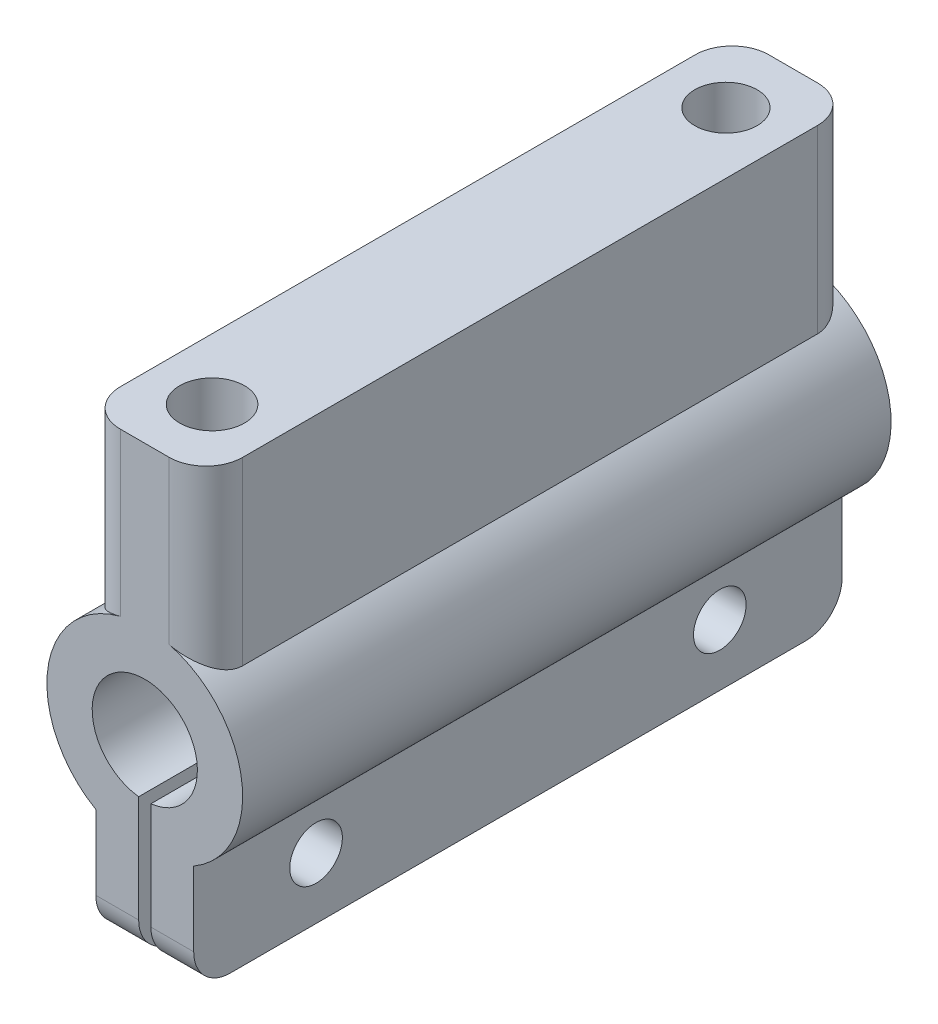
SolidWorks part; units mm, degrees
material "Ti-5Al-2.5Sn Annealed (SS)"
ref_plane "前视基准面" through (0, 0, 0) normal (0, 0, 1) x (1, 0, 0)
ref_plane "上视基准面" through (0, 0, 0) normal (0, 1, 0) x (1, 0, 0)
ref_plane "右视基准面" through (0, 0, 0) normal (1, 0, 0) x (0, 0, -1)
other "Configuration Table"
sketch "Sketch1" plane through (0, 0, 0) normal (0, 0, 1) x (1, 0, 0)
  line L0 (-8, 25) -> (0, 25)
  line L1 (-8, 25) -> (-8, 9)
  line L2 (-8, 9) -> (0, 9)
  line L3 (0, 25) -> (0, 9)
  line L4 (-4.5, 9) -> (-3.5, 9)
  line L5 (-4.5, 9) -> (-4.5, 25)
  line L6 (-4.5, 25) -> (-3.5, 25)
  line L7 (-3.5, 9) -> (-3.5, 25)
  line L8 (-9, 31.245) -> (1, 31.245)
  line L9 (1, 31.245) -> (1, 46)
  line L10 (1, 46) -> (-9, 46)
  line L11 (-9, 46) -> (-9, 31.245)
  circle A0 centre (-4, 25) radius 8
  circle A1 centre (-4, 25) radius 4.3
  point P11 (-4, 9)
  dimension "D1" = 16
  dimension "D2" = 8.6
  dimension "D3" = 3.5
  dimension "D4" = 4
  dimension "D5" = 8
  dimension "D6" = 25
  dimension "D7" = 16
  dimension "D8" = 10
  dimension "D9" = 14.755
extrude "Boss-Extrude1" add sketch "Sketch1" along normal blind 53 contours A0 L9 L10 L11 | L8 A0 | A1 L3 A0 L8 L1 | A1 L7 A0 L3 | A1 L1 A0 L5 | A0 L1 L2 L5 | A0 L7 L2 L3
sketch "Sketch2" plane through (0, 0, 0) normal (1, 0, 0) x (0, 0, -1)
  line L0 (-26.5, 9) -> (-26.5, 11.718) construction
  line L2 (-53, 9) -> (0, 9) construction
  line L3 (-53, 18.0718) -> (-53, 9) construction
  circle A0 centre (-43, 14) radius 2.15
  circle A1 centre (-10, 14) radius 2.15
  point P12 (-29.8029, 4.4587)
  dimension "D2" = 5
  dimension "D3" = 4.3
  dimension "D1" = 10
extrude "Cut-Extrude1" cut sketch "Sketch2" against normal blind 40
sketch "Sketch3" plane through (0, 46, 0) normal (0, 1, 0) x (1, 0, 0)
  line L0 (-9, -26.5) -> (1, -26.5) construction
  line L1 (-9, -53) -> (-9, 0) construction
  line L2 (1, -53) -> (1, 0) construction
  line L3 (-9, -53) -> (-9, 0) construction
  circle A0 centre (-4, -5.5) radius 2.55
  circle A1 centre (-4, -47.5) radius 2.65
  point P10 (0, 0)
  point P13 (-3.5928, -5.502)
  point P14 (0.3983, -5.7309)
  point P15 (0, 0)
  dimension "D1" = 5.1
  dimension "D2" = 5.3
  dimension "D3" = 42
  dimension "D4" = 21
  dimension "D5" = 5
extrude "Cut-Extrude2" cut sketch "Sketch3" against normal blind 7
fillet "Fillet1" radius 3 8 edges at (1, 38.6225, 53) (-9, 38.6225, 53) (1, 38.6225, 0) (-9, 38.6225, 0) (-6.25, 9, 0) (-1.75, 9, 0) (-6.25, 9, 53) (-1.75, 9, 53)
